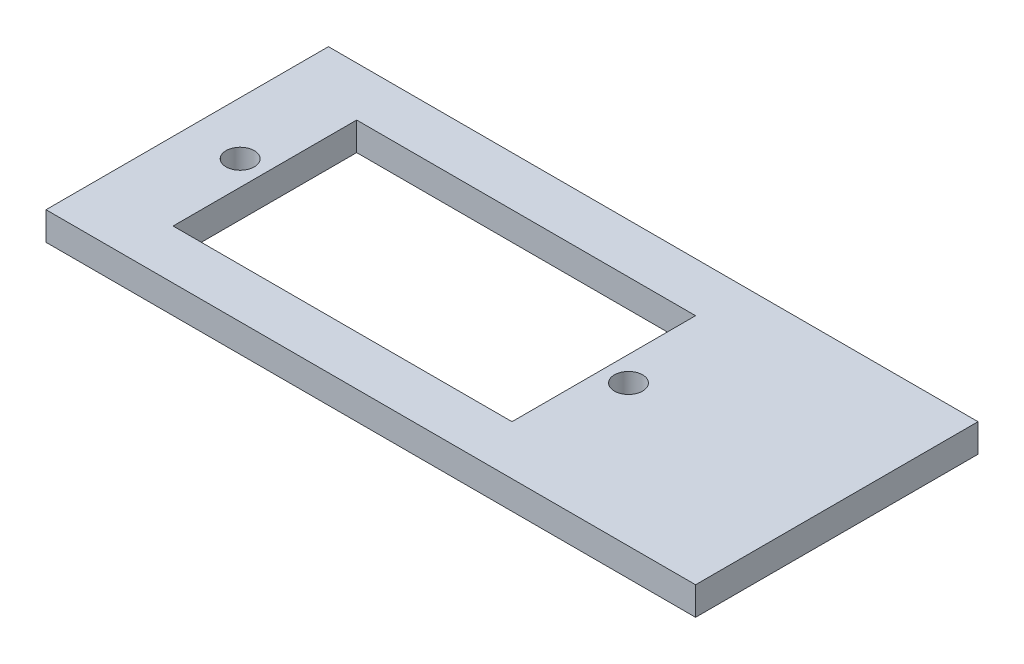
SolidWorks part; units mm, degrees
material "uhlíková ocel 7850"
ref_plane "Přední rovina" through (0, 0, 0) normal (0, 0, 1) x (1, 0, 0)
ref_plane "Horní rovina" through (0, 0, 0) normal (0, 1, 0) x (1, 0, 0)
ref_plane "Pravá rovina" through (0, 0, 0) normal (1, 0, 0) x (0, 0, -1)
sketch "Skica1" plane through (0, 0, 0) normal (0, 1, 0) x (1, 0, 0)
  line L1 (23, -10) -> (-23, -10)
  line L2 (23, -10) -> (23, 10)
  line L3 (23, 10) -> (-23, 10)
  line L4 (-23, -10) -> (-23, 10)
  line L5 (23, -10) -> (-23, 10) construction
  line L6 (23, 10) -> (-23, -10) construction
  point P0 (0, 0)
  dimension "D1" = 20
  dimension "D2" = 46
extrude "Přidat vysunutím1" add sketch "Skica1" along normal blind 2
sketch "Skica2" plane through (0, 2, 0) normal (0, 1, 0) x (1, 0, 0)
  line L0 (-5.5, 0) -> (0, 0) construction
  line L1 (-17.5, -6.5) -> (6.5, -6.5)
  line L2 (-17.5, -6.5) -> (-17.5, 6.5)
  line L3 (-17.5, 6.5) -> (6.5, 6.5)
  line L4 (6.5, -6.5) -> (6.5, 6.5)
  line L5 (-17.5, -6.5) -> (6.5, 6.5) construction
  line L6 (-17.5, 6.5) -> (6.5, -6.5) construction
  line L7 (-23, 10) -> (-23, -10) construction
  point P0 (-5.5, 0)
  dimension "D1" = 13
  dimension "D2" = 24
  dimension "D3" = 5.5
extrude "Odebrat vysunutím1" cut sketch "Skica2" against normal blind 2
sketch "Skica3" plane through (0, 2, 0) normal (0, 1, 0) x (1, 0, 0)
  line L0 (-19.25, 0) -> (8.25, 0) construction
  line L1 (-5.5, 0) -> (-5.5, 6.5) construction
  line L2 (6.5, 6.5) -> (-17.5, 6.5) construction
  circle A0 centre (-19.25, 0) radius 1
  circle A1 centre (8.25, 0) radius 1
  dimension "D2" = 2
  dimension "D1" = 27.5
extrude "Odebrat vysunutím2" cut sketch "Skica3" against normal blind 2
